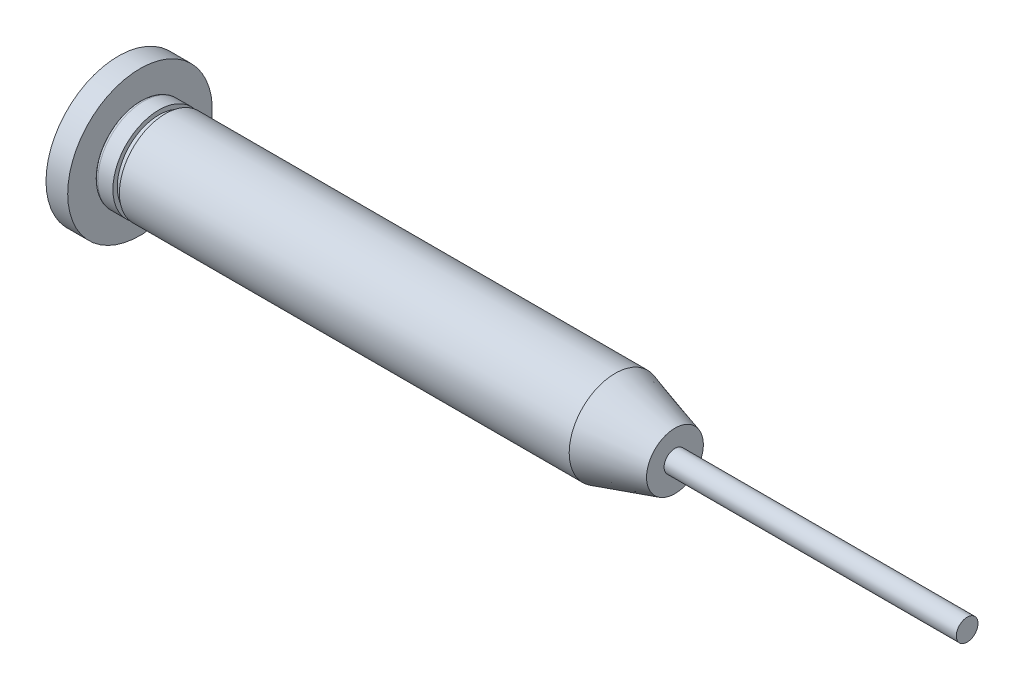
SolidWorks part; units mm, degrees
ref_plane "Front Plane" through (0, 0, 0) normal (0, 0, 1) x (1, 0, 0)
ref_plane "Top Plane" through (0, 0, 0) normal (0, 1, 0) x (1, 0, 0)
ref_plane "Right Plane" through (0, 0, 0) normal (1, 0, 0) x (0, 0, -1)
sketch "Sketch1" plane through (0, 0, 0) normal (0, 0, 1) x (1, 0, 0)
  line L0 (16.42, 1.5875) -> (20.5559, 0.375)
  line L1 (-16.42, 1.5875) -> (-15.12, 1.5875)
  line L2 (-16.42, 1.5875) -> (-16.42, -1.5875)
  line L3 (-16.42, -1.5875) -> (16.42, -1.5875)
  line L4 (-15.12, 1.5875) -> (-15.12, 1.2875)
  line L5 (-16.42, 1.5875) -> (16.42, -1.5875) construction
  line L6 (-16.42, -1.5875) -> (16.42, 1.5875) construction
  line L8 (16.42, -1.5875) -> (20.5559, -0.375)
  line L12 (-15.12, 1.2875) -> (-14.67, 1.2875)
  line L13 (-14.67, 1.2875) -> (-14.67, 1.5875)
  line L14 (-14.67, 1.5875) -> (16.42, 1.5875)
  line L15 (20.5559, 0.375) -> (20.5559, -0.375)
  point P0 (0, 0)
  dimension "D1" = 32.84
  dimension "D2" = 3.175
  dimension "D6" = 0.3
  dimension "D7" = 0.45
  dimension "D8" = 1.3
revolve "Revolve1" add sketch "Sketch1" angle 360 about L3
fillet "Fillet1" radius 0.25 1 edges at (-16.42, -1.5875, 3.175)
sketch "Sketch2" plane through (0, 0, 0) normal (0, 0, 1) x (1, 0, 0)
  line L0 (20.5559, -1.5875) -> (40.7559, -1.5875)
  line L1 (20.5559, -3.55) -> (20.5559, 0.375) construction
  line L2 (40.7559, -1.5875) -> (40.7559, -0.8375)
  line L3 (40.7559, -0.8375) -> (20.5559, -0.8375)
  line L4 (20.5559, -0.8375) -> (20.5559, -1.5875)
  dimension "D1" = 0.75
  dimension "D2" = 20.2
revolve "Revolve2" add sketch "Sketch2" angle 360 about L0
sketch "Sketch3" plane through (20.5559, 0, 0) normal (1, 0, 0) x (0, 0, -1)
  circle A0 centre (0, -1.5875) radius 1.2125
extrude "Boss-Extrude1" add sketch "Sketch3" against normal blind 10
sketch "Sketch4" plane through (-16.42, 0, 0) normal (-1, 0, 0) x (0, 0, 1)
  circle A0 centre (0, -1.5875) radius 1.5
  dimension "D1" = 3
extrude "Cut-Extrude1" cut sketch "Sketch4" against normal blind 15
sketch "Sketch6" plane through (-16.42, 0, 0) normal (-1, 0, 0) x (0, 0, 1)
  circle A0 centre (0, -1.5875) radius 5
  dimension "D1" = 10
extrude "Boss-Extrude2" add sketch "Sketch6" along normal blind 1.5
